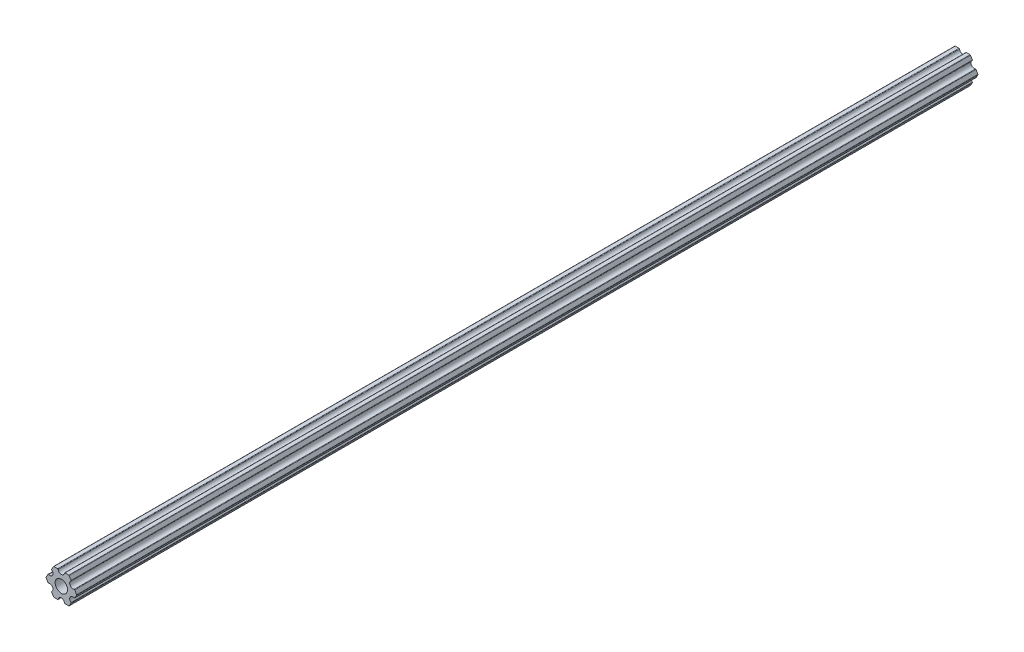
SolidWorks part; units mm, degrees
material "6063-O"
ref_plane "Front Plane" through (0, 0, 0) normal (0, 0, 1) x (1, 0, 0)
ref_plane "Top Plane" through (0, 0, 0) normal (0, 1, 0) x (1, 0, 0)
ref_plane "Right Plane" through (0, 0, 0) normal (1, 0, 0) x (0, 0, -1)
sketch "Sketch1" plane through (0, 0, 0) normal (0, 0, 1) x (1, 0, 0)
  line L0 (0, 0) -> (12.3002, 0) construction
  line L1 (7.3323, 0) -> (3.6662, 6.35)
  line L2 (3.6662, 6.35) -> (-3.6662, 6.35)
  line L3 (-3.6662, 6.35) -> (-7.3323, 0)
  line L4 (-7.3323, 0) -> (-3.6662, -6.35)
  line L5 (-3.6662, -6.35) -> (3.6662, -6.35)
  line L6 (3.6662, -6.35) -> (7.3323, 0)
  circle A0 centre (0, 0) radius 6.35 construction
  circle A24 centre (0, 0) radius 2.9337
  dimension "D1" = 5.8674
  dimension "D2" = 12.7
extrude "Extrude1" add sketch "Sketch1" against normal mid plane 428.625
sketch "Sketch5" plane through (0, 0, 214.3125) normal (0, 0, 1) x (1, 0, 0)
  line L0 (3.6662, 6.35) -> (-3.6662, 6.35) construction
  circle A0 centre (0, 6.35) radius 1.524
  dimension "D1" = 3.048
extrude "Extrude2" cut sketch "Sketch5" against normal through all
pattern_circular "CirPattern2" count 6 over 360 about axis through (0, 0, 0) along (0, 0, 1) of "Extrude2"
fillet "Fillet1" radius 0.254 18 edges at (4.7373, 4.4948, 0) (6.2613, 1.8552, 0) (-1.524, 6.35, 0) (1.524, 6.35, 0) (7.3323, 0, 0) (6.2613, -1.8552, 0) (4.7373, -4.4948, 0) (3.6662, -6.35, 0) (1.524, -6.35, 0) (-1.524, -6.35, 0) (-3.6662, -6.35, 0) (-4.7373, -4.4948, 0) (-6.2613, -1.8552, 0) (-7.3323, 0, 0) (-6.2613, 1.8552, 0) (-4.7373, 4.4948, 0) (-3.6662, 6.35, 0) (3.6662, 6.35, 0)
sketch "Sketch6" [suppressed] plane through (0, 0, 214.3125) normal (0, 0, 1) x (1, 0, 0)
  line L12 (7.259, 0.127) -> (6.3791, 1.651)
  line L13 (4.6194, 4.699) -> (3.7395, 6.223)
  line L14 (3.5195, 6.35) -> (1.7598, 6.35)
  line L15 (-1.7598, 6.35) -> (-3.5195, 6.35)
  line L16 (-3.7395, 6.223) -> (-4.6194, 4.699)
  line L17 (-6.3791, 1.651) -> (-7.259, 0.127)
  line L18 (-7.259, -0.127) -> (-6.3791, -1.651)
  line L19 (-4.6194, -4.699) -> (-3.7395, -6.223)
  line L20 (-3.5195, -6.35) -> (-1.7598, -6.35)
  line L21 (1.7598, -6.35) -> (3.5195, -6.35)
  line L22 (3.7395, -6.223) -> (4.6194, -4.699)
  line L23 (6.3791, -1.651) -> (7.259, -0.127)
  line L24 (7.259, 0.127) -> (6.3791, 1.651)
  line L25 (4.6194, 4.699) -> (3.7395, 6.223)
  line L26 (3.5195, 6.35) -> (1.7598, 6.35)
  line L27 (-1.7598, 6.35) -> (-3.5195, 6.35)
  line L28 (-3.7395, 6.223) -> (-4.6194, 4.699)
  line L29 (-6.3791, 1.651) -> (-7.259, 0.127)
  line L30 (-7.259, -0.127) -> (-6.3791, -1.651)
  line L31 (-4.6194, -4.699) -> (-3.7395, -6.223)
  line L32 (-3.5195, -6.35) -> (-1.7598, -6.35)
  line L33 (1.7598, -6.35) -> (3.5195, -6.35)
  line L34 (3.7395, -6.223) -> (4.6194, -4.699)
  line L35 (6.3791, -1.651) -> (7.259, -0.127)
  circle A0 centre (0, 0) radius 2.9337 construction
  circle A1 centre (0, 0) radius 2.9337
  arc A24 (6.3791, 1.651) -> (6.0649, 1.7599) centre (6.1592, 1.524) ccw
  arc A25 (4.5565, 4.3724) -> (6.0649, 1.7599) centre (5.4993, 3.175) ccw
  arc A26 (4.5565, 4.3724) -> (4.6194, 4.699) centre (4.3994, 4.572) ccw
  arc A27 (3.7395, 6.223) -> (3.5195, 6.35) centre (3.5195, 6.096) ccw
  arc A28 (1.7598, 6.35) -> (1.5084, 6.1323) centre (1.7598, 6.096) ccw
  arc A29 (-1.5084, 6.1323) -> (1.5084, 6.1323) centre (0, 6.35) ccw
  arc A30 (-1.5084, 6.1323) -> (-1.7598, 6.35) centre (-1.7598, 6.096) ccw
  arc A31 (-3.5195, 6.35) -> (-3.7395, 6.223) centre (-3.5195, 6.096) ccw
  arc A32 (-4.6194, 4.699) -> (-4.5565, 4.3724) centre (-4.3994, 4.572) ccw
  arc A33 (-6.0649, 1.7599) -> (-4.5565, 4.3724) centre (-5.4993, 3.175) ccw
  arc A34 (-6.0649, 1.7599) -> (-6.3791, 1.651) centre (-6.1592, 1.524) ccw
  arc A35 (-7.259, 0.127) -> (-7.259, -0.127) centre (-7.0391, 0) ccw
  arc A36 (-6.3791, -1.651) -> (-6.0649, -1.7599) centre (-6.1592, -1.524) ccw
  arc A37 (-4.5565, -4.3724) -> (-6.0649, -1.7599) centre (-5.4993, -3.175) ccw
  arc A38 (-4.5565, -4.3724) -> (-4.6194, -4.699) centre (-4.3994, -4.572) ccw
  arc A39 (-3.7395, -6.223) -> (-3.5195, -6.35) centre (-3.5195, -6.096) ccw
  arc A40 (-1.7598, -6.35) -> (-1.5084, -6.1323) centre (-1.7598, -6.096) ccw
  arc A41 (1.5084, -6.1323) -> (-1.5084, -6.1323) centre (0, -6.35) ccw
  arc A42 (1.5084, -6.1323) -> (1.7598, -6.35) centre (1.7598, -6.096) ccw
  arc A43 (3.5195, -6.35) -> (3.7395, -6.223) centre (3.5195, -6.096) ccw
  arc A44 (4.6194, -4.699) -> (4.5565, -4.3724) centre (4.3994, -4.572) ccw
  arc A45 (6.0649, -1.7599) -> (4.5565, -4.3724) centre (5.4993, -3.175) ccw
  arc A46 (6.0649, -1.7599) -> (6.3791, -1.651) centre (6.1592, -1.524) ccw
  arc A47 (7.259, -0.127) -> (7.259, 0.127) centre (7.0391, 0) ccw
  arc A48 (6.3791, 1.651) -> (6.0649, 1.7599) centre (6.1592, 1.524) ccw
  arc A49 (4.5565, 4.3724) -> (6.0649, 1.7599) centre (5.4993, 3.175) ccw
  arc A50 (4.5565, 4.3724) -> (4.6194, 4.699) centre (4.3994, 4.572) ccw
  arc A51 (3.7395, 6.223) -> (3.5195, 6.35) centre (3.5195, 6.096) ccw
  arc A52 (1.7598, 6.35) -> (1.5084, 6.1323) centre (1.7598, 6.096) ccw
  arc A53 (-1.5084, 6.1323) -> (1.5084, 6.1323) centre (0, 6.35) ccw
  arc A54 (-1.5084, 6.1323) -> (-1.7598, 6.35) centre (-1.7598, 6.096) ccw
  arc A55 (-3.5195, 6.35) -> (-3.7395, 6.223) centre (-3.5195, 6.096) ccw
  arc A56 (-4.6194, 4.699) -> (-4.5565, 4.3724) centre (-4.3994, 4.572) ccw
  arc A57 (-6.0649, 1.7599) -> (-4.5565, 4.3724) centre (-5.4993, 3.175) ccw
  arc A58 (-6.0649, 1.7599) -> (-6.3791, 1.651) centre (-6.1592, 1.524) ccw
  arc A59 (-7.259, 0.127) -> (-7.259, -0.127) centre (-7.0391, 0) ccw
  arc A60 (-6.3791, -1.651) -> (-6.0649, -1.7599) centre (-6.1592, -1.524) ccw
  arc A61 (-4.5565, -4.3724) -> (-6.0649, -1.7599) centre (-5.4993, -3.175) ccw
  arc A62 (-4.5565, -4.3724) -> (-4.6194, -4.699) centre (-4.3994, -4.572) ccw
  arc A63 (-3.7395, -6.223) -> (-3.5195, -6.35) centre (-3.5195, -6.096) ccw
  arc A64 (-1.7598, -6.35) -> (-1.5084, -6.1323) centre (-1.7598, -6.096) ccw
  arc A65 (1.5084, -6.1323) -> (-1.5084, -6.1323) centre (0, -6.35) ccw
  arc A66 (1.5084, -6.1323) -> (1.7598, -6.35) centre (1.7598, -6.096) ccw
  arc A67 (3.5195, -6.35) -> (3.7395, -6.223) centre (3.5195, -6.096) ccw
  arc A68 (4.6194, -4.699) -> (4.5565, -4.3724) centre (4.3994, -4.572) ccw
  arc A69 (6.0649, -1.7599) -> (4.5565, -4.3724) centre (5.4993, -3.175) ccw
  arc A70 (6.0649, -1.7599) -> (6.3791, -1.651) centre (6.1592, -1.524) ccw
  arc A71 (7.259, -0.127) -> (7.259, 0.127) centre (7.0391, 0) ccw
  dimension "D1" = 0
extrude "Extrude3" [suppressed] add sketch "Sketch6" along normal blind 254
